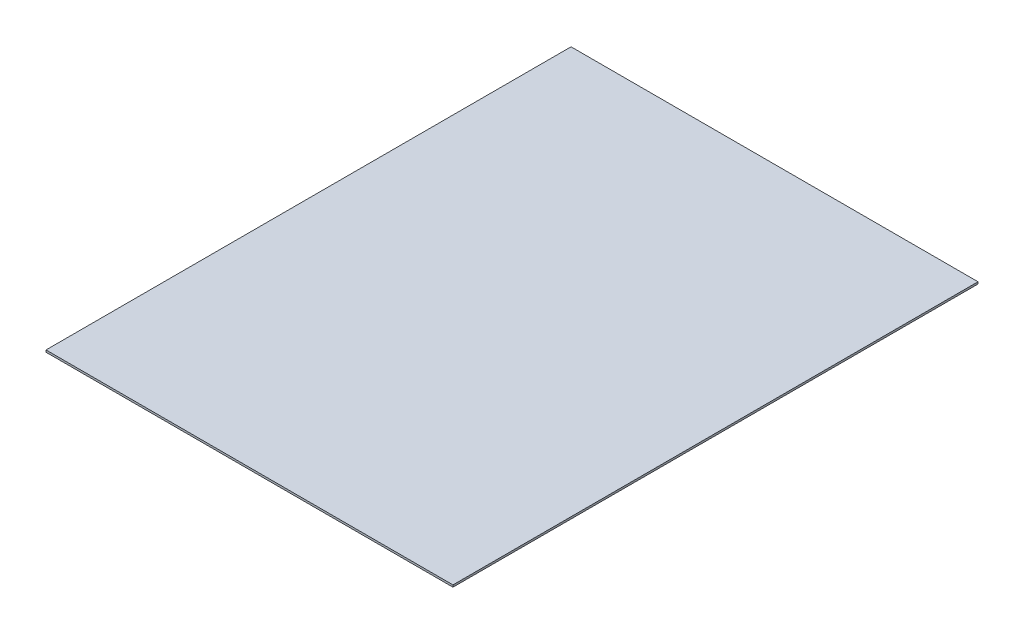
SolidWorks part; units mm, degrees
material "Teak"
ref_plane "Front Plane" through (0, 0, 0) normal (0, 0, 1) x (1, 0, 0)
ref_plane "Top Plane" through (0, 0, 0) normal (0, 1, 0) x (1, 0, 0)
ref_plane "Right Plane" through (0, 0, 0) normal (1, 0, 0) x (0, 0, -1)
sketch "Sketch1" plane through (0, 0, 0) normal (0, 1, 0) x (1, 0, 0)
  line L1 (-563.5625, -727.075) -> (563.5625, -727.075)
  line L2 (-563.5625, -727.075) -> (-563.5625, 727.075)
  line L3 (-563.5625, 727.075) -> (563.5625, 727.075)
  line L4 (563.5625, -727.075) -> (563.5625, 727.075)
  line L5 (-563.5625, -727.075) -> (563.5625, 727.075) construction
  line L6 (-563.5625, 727.075) -> (563.5625, -727.075) construction
  point P0 (0, 0)
  dimension "D1" = 1127.125
  dimension "D2" = 1454.15
extrude "Boss-Extrude1" add sketch "Sketch1" along normal blind 5.5562
